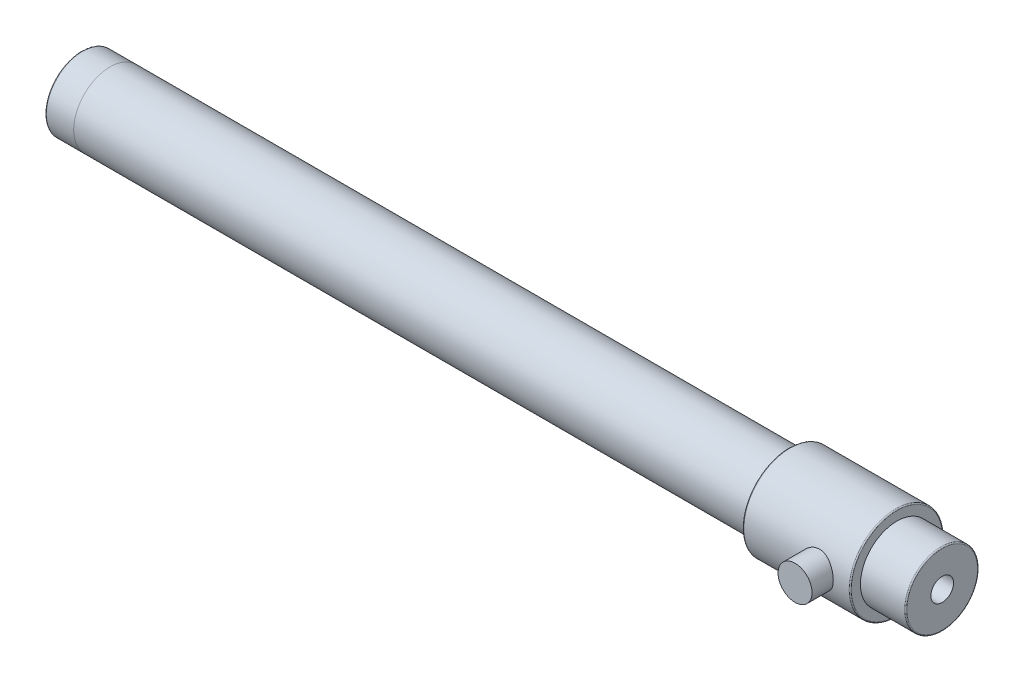
SolidWorks part; units mm, degrees
material "1100-H26 pręt (SS)"
ref_plane "Płaszczyzna XY" through (0, 0, 0) normal (0, 0, 1) x (1, 0, 0)
ref_plane "Płaszczyzna XZ" through (0, 0, 0) normal (0, 1, 0) x (1, 0, 0)
ref_plane "Płaszczyzna YZ" through (0, 0, 0) normal (1, 0, 0) x (0, 0, -1)
sketch "Szkic1" plane through (0, 0, 0) normal (0, 0, 1) x (1, 0, 0)
  line L0 (0, 0) -> (152, 0) construction
  line L1 (0, 2) -> (152, 2)
  line L2 (0, 2) -> (0, 6.45)
  line L3 (0, 6.45) -> (125, 6.45)
  line L4 (125, 6.45) -> (125, 8.25)
  line L5 (125, 8.25) -> (144, 8.25)
  line L6 (144, 8.25) -> (144, 6.45)
  line L7 (144, 6.45) -> (152, 6.45)
  line L8 (152, 6.45) -> (152, 2)
  dimension "D1" = 152
  dimension "D2" = 4
  dimension "D3" = 19
  dimension "D4" = 8
  dimension "D5" = 12.9
  dimension "D6" = 16.5
revolve "Obrót1" add sketch "Szkic1" angle 360 about L0
ref_plane "Płaszczyzna1" through (5, 0, 0) normal (-1, 0, 0) x (0, 0, 1)
split line "Linia podziałowa2"
fillet "Zaokrąglenie1" radius 0.2 4 edges at (0, 0, 6.45) (152, 0, 6.45) (144, 0, 8.25) (125, 0, 8.25)
ref_plane "Płaszczyzna2" through (0, 0, 2) normal (0, 0, -1) x (-1, 0, 0)
sketch "Szkic3" plane through (0, 0, 2) normal (0, 0, -1) x (-1, 0, 0)
  line L0 (-152, 6.25) -> (-152, -6.25) construction
  circle A0 centre (-138, 0) radius 3
  dimension "D1" = 6
  dimension "D2" = 14
extrude "Dodanie-wyciągnięcie1" add sketch "Szkic3" against normal blind 10
